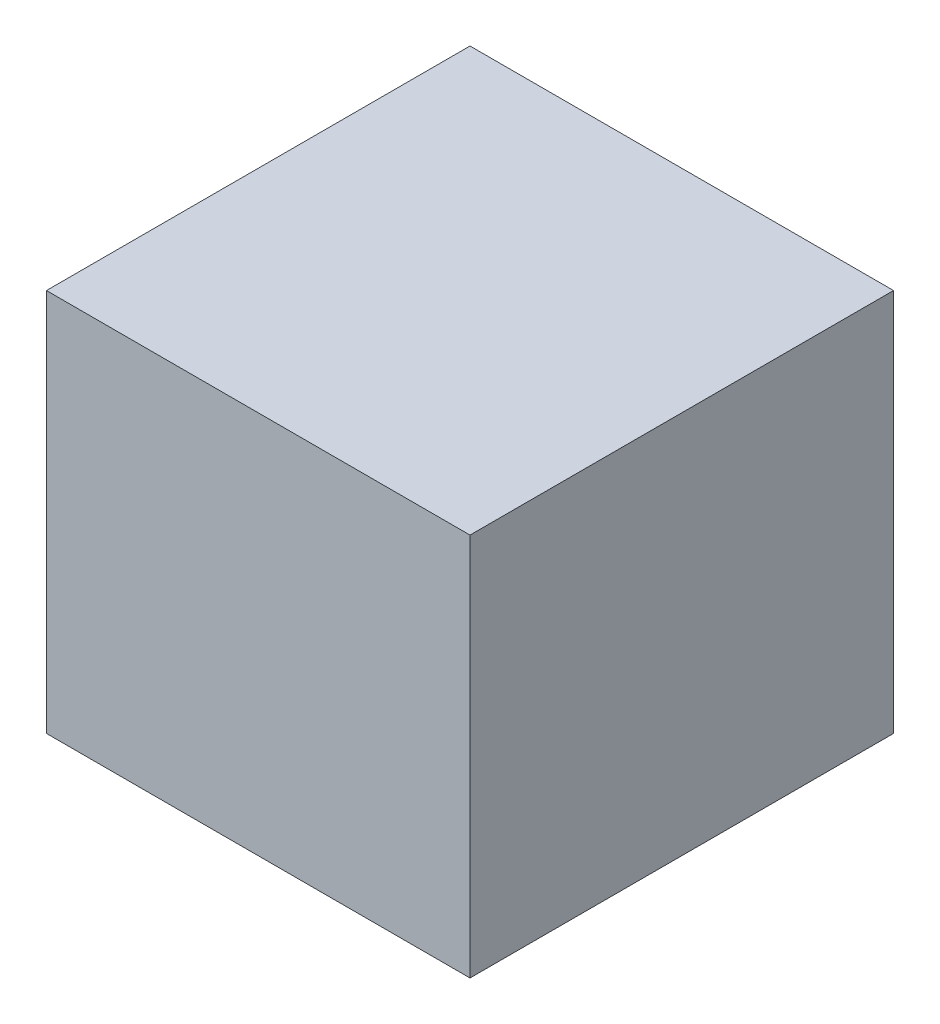
SolidWorks part; units mm, degrees
ref_plane "Front Plane" through (0, 0, 0) normal (0, 0, 1) x (1, 0, 0)
ref_plane "Top Plane" through (0, 0, 0) normal (0, 1, 0) x (1, 0, 0)
ref_plane "Right Plane" through (0, 0, 0) normal (1, 0, 0) x (0, 0, -1)
sketch "Sketch1" plane through (0, 0, 0) normal (0, 1, 0) x (1, 0, 0)
  line L1 (-15.9, -15.9) -> (15.9, -15.9)
  line L2 (-15.9, -15.9) -> (-15.9, 15.9)
  line L3 (-15.9, 15.9) -> (15.9, 15.9)
  line L4 (15.9, -15.9) -> (15.9, 15.9)
  line L5 (-15.9, -15.9) -> (15.9, 15.9) construction
  line L6 (-15.9, 15.9) -> (15.9, -15.9) construction
  point P0 (0, 0)
  dimension "D1" = 31.8
extrude "Boss-Extrude1" add sketch "Sketch1" along normal blind 28.8
